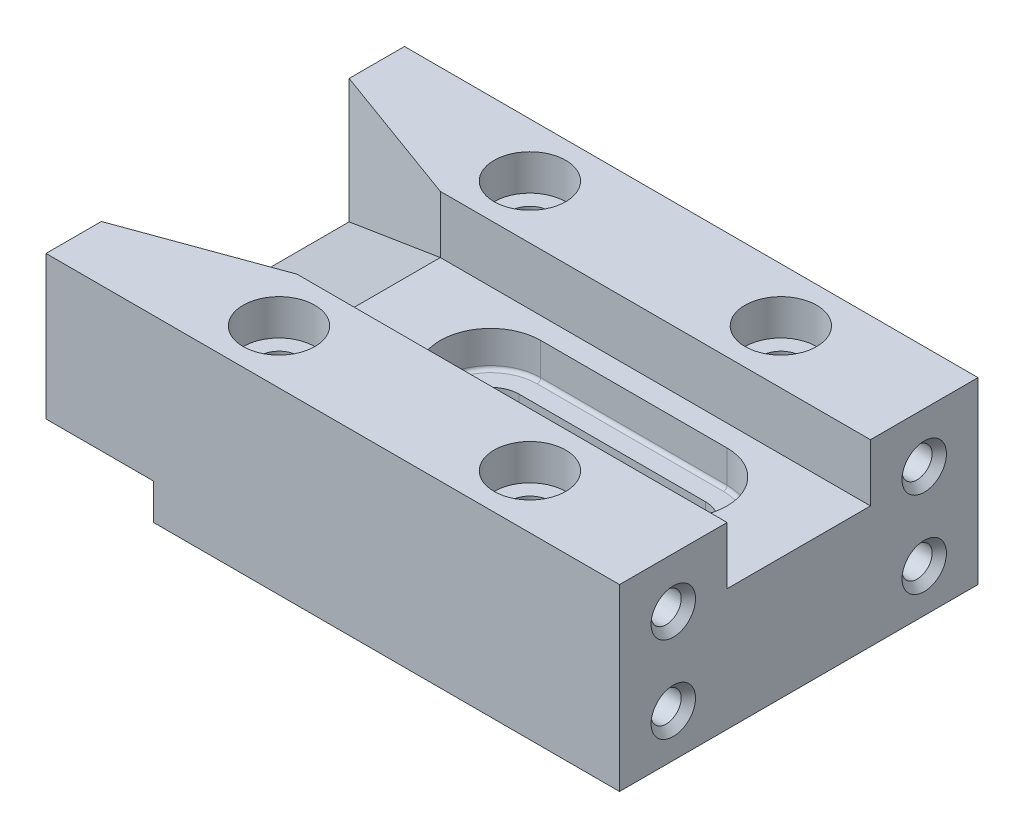
SolidWorks part; units mm, degrees
ref_plane "Přední rovina" through (0, 0, 0) normal (0, 0, 1) x (1, 0, 0)
ref_plane "Vrchní rovina" through (0, 0, 0) normal (0, 1, 0) x (1, 0, 0)
ref_plane "Pravá rovina" through (0, 0, 0) normal (1, 0, 0) x (0, 0, -1)
sketch "Skica1" plane through (0, 0, 0) normal (0, 0, 1) x (1, 0, 0)
  line L1 (-40, -12.5) -> (40, -12.5)
  line L2 (-40, -12.5) -> (-40, 12.5)
  line L3 (-40, 12.5) -> (40, 12.5)
  line L4 (40, -12.5) -> (40, 12.5)
  line L5 (-40, -12.5) -> (40, 12.5) construction
  line L6 (-40, 12.5) -> (40, -12.5) construction
  point P0 (0, 0)
  dimension "D1" = 80
  dimension "D2" = 25
extrude "Přidat vysunutím1" add sketch "Skica1" along normal mid plane 50
sketch "Skica2" plane through (0, 0, 25) normal (0, 0, 1) x (1, 0, 0)
  line L0 (-40, 12.5) -> (-40, -12.5) construction
  line L1 (-40, -7.5) -> (-25, -7.5)
  line L2 (-40, -7.5) -> (-40, -12.5)
  line L3 (-40, -12.5) -> (-25, -12.5)
  line L4 (-25, -7.5) -> (-25, -12.5)
  line L5 (-40, -12.5) -> (40, -12.5) construction
  dimension "D1" = 5
  dimension "D2" = 15
extrude "Odebrat vysunutím1" cut sketch "Skica2" against normal through all
sketch "Skica3" plane through (0, 12.5, 0) normal (0, 1, 0) x (1, 0, 0)
  line L0 (-40, 0) -> (40, 0) construction
  line L1 (-40, -25) -> (-40, 25) construction
  line L2 (40, -25) -> (40, 25) construction
  line L3 (-40, 17.2794) -> (-20, 10)
  line L4 (-20, 10) -> (40, 10)
  line L5 (40, 10) -> (40, -10)
  line L6 (40, -10) -> (-20, -10)
  line L7 (-20, -10) -> (-40, -17.2794)
  line L8 (-40, -17.2794) -> (-40, 17.2794)
  dimension "D1" = 40
  dimension "D2" = 20
  dimension "D3" = 60
extrude "Odebrat vysunutím2" cut sketch "Skica3" against normal blind 8
chamfer "Zkosení1" distance 20 angle 25 1 edges at (-40, 4.5, 0)
sketch "Skica4" plane through (0, 4.5, 0) normal (0, 1, 0) x (1, 0, 0)
  line L0 (40, 0) -> (-20, 0) construction
  line L1 (40, -10) -> (40, 10) construction
  line L2 (-20, 10) -> (-20, -10) construction
  line L3 (-3, 0) -> (23, 0) construction
  line L4 (-3, 7) -> (23, 7)
  line L5 (-3, -7) -> (23, -7)
  arc A0 (-3, 7) -> (-3, -7) centre (-3, 0) ccw
  arc A1 (23, -7) -> (23, 7) centre (23, 0) ccw
  point P8 (10, 0)
  dimension "D2" = 17
  dimension "D3" = 7
  dimension "D1" = 26
extrude "Odebrat vysunutím3" cut sketch "Skica4" against normal blind 5
sketch "Skica5" plane through (0, -0.5, 0) normal (0, 1, 0) x (1, 0, 0)
  line L10 (-3, -4) -> (23, -4)
  line L11 (23, 4) -> (-3, 4)
  line L12 (-3, -4) -> (23, -4)
  line L13 (23, 4) -> (-3, 4)
  arc A8 (-3, 4) -> (-3, -4) centre (-3, 0) ccw
  arc A9 (23, -4) -> (23, 4) centre (23, 0) ccw
  arc A10 (-3, 4) -> (-3, -4) centre (-3, 0) ccw
  arc A11 (23, -4) -> (23, 4) centre (23, 0) ccw
  dimension "D1" = 3
extrude "Odebrat vysunutím4" cut sketch "Skica5" against normal through all
sketch "Skica6" plane through (0, 12.5, 0) normal (0, 1, 0) x (1, 0, 0)
  line L0 (40, 0) -> (-40, 0) construction
  line L1 (40, -10) -> (40, 10) construction
  line L2 (-40, -17.2794) -> (-40, 17.2794) construction
  line L3 (40, 10) -> (40, 25) construction
  point P0 (20, 17.5)
  point P1 (-15, 17.5)
  point P2 (-15, -17.5)
  point P3 (20, -17.5)
  dimension "D1" = 35
  dimension "D2" = 20
  dimension "D3" = 35
hole_wizard "Díra1" positions "Skica7" profile "Skica8" legacy end condition through all
sketch "Skica7" plane through (0, 12.5, 0) normal (0, 1, 0) x (1, 0, 0)
  point P0 (-15, 17.5)
  point P3 (20, 17.5)
  point P6 (20, -17.5)
  point P9 (-15, -17.5)
sketch "Skica8" plane through (-15, 12.5, -17.5) normal (1, 0, 0) x (0, 0, 1)
  line L0 (0, 0) -> (0, 26.6524)
  line L1 (0, 26.6524) -> (2.75, 25)
  line L2 (2.75, 25) -> (2.75, 5)
  line L3 (2.75, 5) -> (5, 5)
  line L4 (5, 0) -> (0, 0)
  line L5 (0, -11.3109) -> (0, 121.1557) construction
  line L6 (0, 26.6524) -> (-2.75, 25) construction
  line L7 (5, 5) -> (5, 0)
  dimension "Průměr" = 5.5
  dimension "Hloubka" = 25
  dimension "Průměr válc. zahloubení" = 10
  dimension "Hloubka válc. zahloubení" = 5
  dimension "Úhel vrtání" = 118
sketch "Skica9" plane through (40, 0, 0) normal (1, 0, 0) x (0, 0, -1)
  line L0 (0, 4.5) -> (0, -12.5) construction
  line L1 (-10, 4.5) -> (10, 4.5) construction
  line L2 (-25, -12.5) -> (25, -12.5) construction
  line L3 (-25, 12.5) -> (-10, 12.5) construction
  point P0 (-17.5, 5.5)
  point P1 (-17.5, -6.5)
  point P2 (17.5, 5.5)
  point P3 (17.5, -6.5)
  dimension "D1" = 35
  dimension "D2" = 7
  dimension "D3" = 12
hole_wizard "M5 závit1" positions "Skica10" profile "Skica11" tap size "M5" standard "ISO"
sketch "Skica10" plane through (40, 0, 0) normal (1, 0, 0) x (0, 0, -1)
  point P0 (-17.5, 5.5)
  point P3 (-17.5, -6.5)
  point P6 (17.5, 5.5)
  point P9 (17.5, -6.5)
sketch "Skica11" plane through (40, 5.5, 17.5) normal (0, 1, 0) x (0, 0, -1)
  line L0 (0, 0) -> (0, 15.2618)
  line L1 (0, 15.2618) -> (2.1, 14)
  line L2 (2.1, 14) -> (2.1, 0)
  line L5 (2.1, 0) -> (0, 0)
  line L10 (0, 15.2618) -> (-2.1, 14) construction
  line L11 (0, -6.35) -> (0, 107.95) construction
  dimension "Průměr závitníku" = 4.2
  dimension "Hloubka závitníku" = 14
  dimension "Úhel vrtání" = 118
cosmetic thread "Závit díry1" parameters "D1"=10, "D2"=5
cosmetic thread "Závit díry2" parameters "D1"=10, "D2"=5
cosmetic thread "Závit díry3" parameters "D1"=10, "D2"=5
cosmetic thread "Závit díry4" parameters "D1"=10, "D2"=5
chamfer "Zkosení2" distance 1 angle 45 4 edges at (40, -6.5, 15.4) (40, -6.5, -19.6) (40, 5.5, -19.6) (40, 5.5, 15.4)
fillet "Zaoblit1" radius 0.5 4 edges at (10, -0.5, -7) (30, -0.5, 0) (10, -0.5, 7) (-10, -0.5, 0)
